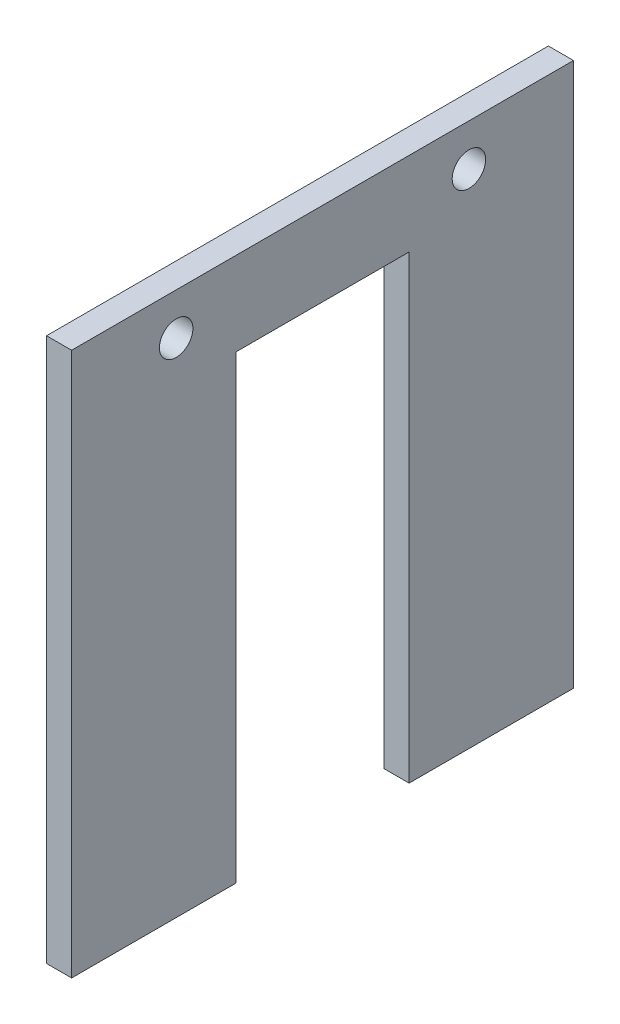
SolidWorks part; units mm, degrees
ref_plane "Front Plane" through (0, 0, 0) normal (0, 0, 1) x (1, 0, 0)
ref_plane "Top Plane" through (0, 0, 0) normal (0, 1, 0) x (1, 0, 0)
ref_plane "Right Plane" through (0, 0, 0) normal (1, 0, 0) x (0, 0, -1)
sketch "Sketch2" plane through (0, 0, 0) normal (1, 0, 0) x (0, 0, -1)
  line L0 (60, 65) -> (0, 65)
  line L1 (12.5, 60) -> (47.5, 60) construction
  line L3 (60, 0) -> (60, 65)
  line L28 (40.35, 0) -> (60, 0)
  line L29 (0, 0) -> (0, 65)
  line L30 (40.35, 0) -> (40.35, 55)
  line L31 (40.35, 55) -> (19.65, 55)
  line L32 (19.65, 55) -> (19.65, 0)
  line L33 (19.65, 0) -> (0, 0)
  circle A0 centre (12.5, 60) radius 2
  circle A1 centre (47.5, 60) radius 2
  point P0 (30, 55)
  point P20 (30, 65)
  point P25 (30, 60)
  dimension "D4" = 4
  dimension "D1" = 20.7
  dimension "D2" = 60
  dimension "D3" = 55
  dimension "D5" = 5
  dimension "D6" = 35
  dimension "D7" = 65
extrude "Boss-Extrude1" add sketch "Sketch2" along normal blind 3
